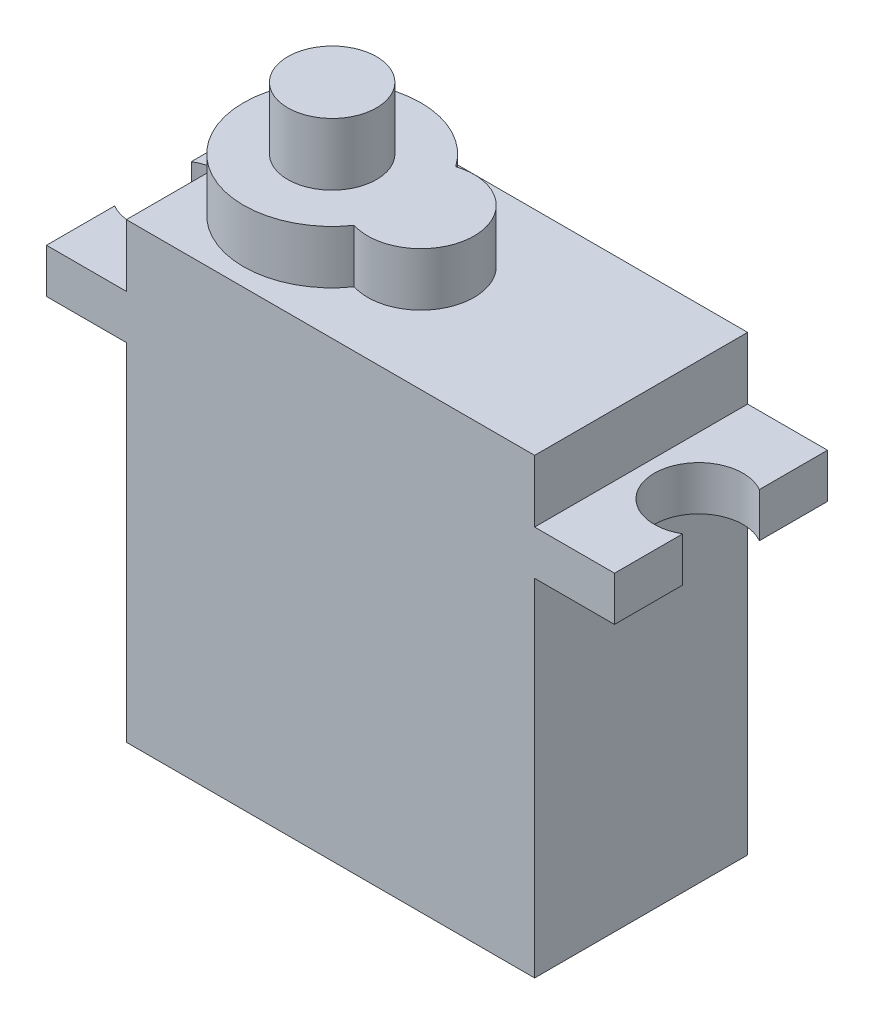
SolidWorks part; units mm, degrees
ref_plane "Alzado" through (0, 0, 0) normal (0, 0, 1) x (1, 0, 0)
ref_plane "Planta" through (0, 0, 0) normal (0, 1, 0) x (1, 0, 0)
ref_plane "Vista lateral" through (0, 0, 0) normal (1, 0, 0) x (0, 0, -1)
sketch "Croquis1" plane through (0, 0, 0) normal (0, 1, 0) x (1, 0, 0)
  line L1 (-11.5, -6) -> (11.5, -6)
  line L2 (-11.5, -6) -> (-11.5, 6)
  line L3 (-11.5, 6) -> (11.5, 6)
  line L4 (11.5, -6) -> (11.5, 6)
  line L5 (-11.5, -6) -> (11.5, 6) construction
  line L6 (-11.5, 6) -> (11.5, -6) construction
  point P0 (0, 0)
  dimension "D1" = 12
  dimension "D2" = 23
extrude "Saliente-Extruir1" add sketch "Croquis1" along normal blind 19.5
sketch "Croquis2" plane through (0, 19.5, 0) normal (0, 1, 0) x (1, 0, 0)
  line L1 (-16, -6) -> (16, -6)
  line L2 (-16, -6) -> (-16, 6)
  line L3 (-16, 6) -> (16, 6)
  line L4 (16, -6) -> (16, 6)
  line L5 (-16, -6) -> (16, 6) construction
  line L6 (-16, 6) -> (16, -6) construction
  point P0 (0, 0)
  dimension "D1" = 12
  dimension "D2" = 32
extrude "Saliente-Extruir2" add sketch "Croquis2" along normal blind 2.5
sketch "Croquis3" plane through (0, 22, 0) normal (0, 1, 0) x (1, 0, 0)
  line L4 (11.5, -6) -> (11.5, 6)
  line L5 (-11.5, -6) -> (11.5, -6)
  line L6 (-11.5, 6) -> (-11.5, -6)
  line L7 (11.5, 6) -> (-11.5, 6)
  line L8 (11.5, -6) -> (11.5, 6)
  line L9 (-11.5, -6) -> (11.5, -6)
  line L10 (-11.5, 6) -> (-11.5, -6)
  line L11 (11.5, 6) -> (-11.5, 6)
  dimension "D1" = 0
extrude "Saliente-Extruir3" add sketch "Croquis3" along normal blind 3.5
sketch "Croquis4" plane through (0, 22, 0) normal (0, 1, 0) x (1, 0, 0)
  line L0 (-16, 6) -> (-16, -6) construction
  line L1 (0, 2.6797) -> (0, -2.7142) construction
  line L2 (-16, 2.161) -> (-16, -2.161)
  line L3 (16, 2.161) -> (16, -2.161)
  line L4 (16, -6) -> (16, 6) construction
  arc A0 (-16, 2.161) -> (-16, -2.161) centre (-14.743, 0) cw
  arc A1 (16, 2.161) -> (16, -2.161) centre (14.743, 0) ccw
  point P14 (16, -2.0838)
  dimension "D1" = 2.5
extrude "Cortar-Extruir1" cut sketch "Croquis4" against normal through all both and the other way through all
sketch "Croquis5" plane through (0, 25.5, 0) normal (0, 1, 0) x (1, 0, 0)
  arc A0 (-1.8059, 2.8618) -> (-1.8059, -2.8618) centre (-5.9059, 0) ccw
  arc A1 (-1.8059, -2.8618) -> (-1.8059, 2.8618) centre (-0.9059, 0) ccw
  point P1 (-2.7834, 0)
  point P3 (0, 0)
  point P4 (-3.3366, 0)
  point P7 (0, 0)
  dimension "D1" = 5
  dimension "D2" = 3
  dimension "5" = 5
extrude "Saliente-Extruir4" add sketch "Croquis5" along normal blind 3
sketch "Croquis6" plane through (0, 28.5, 0) normal (0, 1, 0) x (1, 0, 0)
  circle A0 centre (-5.9059, 0) radius 2.5
  arc A1 (-1.8059, 2.8618) -> (-1.8059, -2.8618) centre (-5.9059, 0) ccw construction
  dimension "D1" = 5
extrude "Saliente-Extruir5" add sketch "Croquis6" along normal blind 3.5
